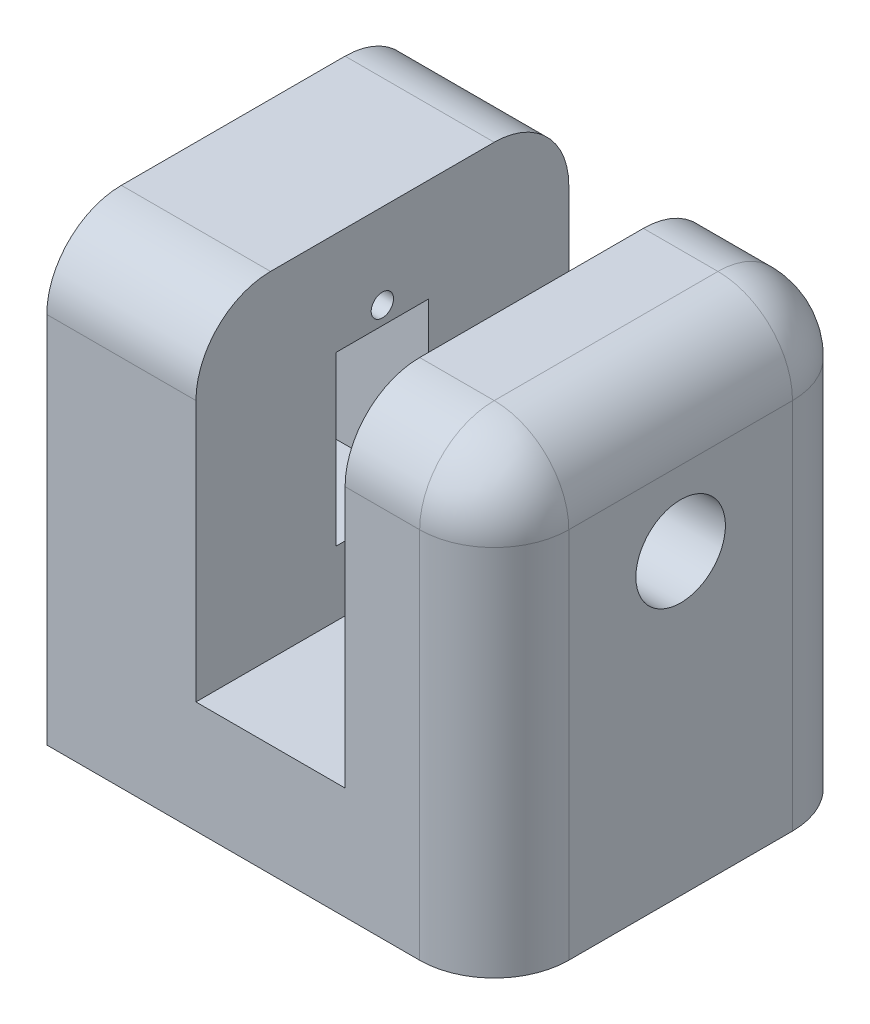
SolidWorks part; units mm, degrees
ref_plane "Front Plane" through (0, 0, 0) normal (0, 0, 1) x (1, 0, 0)
ref_plane "Top Plane" through (0, 0, 0) normal (0, 1, 0) x (1, 0, 0)
ref_plane "Right Plane" through (0, 0, 0) normal (1, 0, 0) x (0, 0, -1)
sketch "Sketch1" plane through (0, 0, 0) normal (0, 1, 0) x (1, 0, 0)
  line L1 (0, 0) -> (60, 0)
  line L2 (0, 0) -> (0, -50)
  line L3 (0, -50) -> (60, -50)
  line L4 (60, 0) -> (60, -50)
extrude "Boss-Extrude1" add sketch "Sketch1" along normal blind 15
sketch "Sketch5" plane through (0, 15, 0) normal (0, 1, 0) x (1, 0, 0)
  line L0 (0, -50) -> (60, -50) construction
  line L1 (0, 0) -> (20, 0)
  line L2 (0, 0) -> (0, -50)
  line L3 (0, -50) -> (20, -50)
  line L4 (20, 0) -> (20, -50)
  line L6 (60, 0) -> (40, 0)
  line L7 (60, 0) -> (60, -50)
  line L8 (60, -50) -> (40, -50)
  line L9 (40, 0) -> (40, -50)
extrude "Boss-Extrude5" add sketch "Sketch5" along normal blind 45
sketch "Sketch6" plane through (0, 0, 0) normal (-1, 0, 0) x (0, 0, 1)
  circle A0 centre (25, 40) radius 6
extrude "Cut-Extrude1" cut sketch "Sketch6" against normal blind 84
sketch "Sketch7" plane through (0, 0, 0) normal (0, -1, 0) x (1, 0, 0)
  circle A0 centre (30, 25) radius 2.5
extrude "Cut-Extrude2" cut sketch "Sketch7" against normal blind 19
fillet "Fillet1" radius 10 4 edges at (10, 60, 50) (50, 60, 50) (50, 60, 0) (10, 60, 0)
fillet "Fillet3" radius 10 5 edges at (60, 25, 0) (60, 57.0711, 2.9289) (60, 60, 25) (60, 57.0711, 47.0711) (60, 25, 50)
sketch "Sketch8" plane through (0, 0, 0) normal (-1, 0, 0) x (0, 0, 1)
  line L2 (25, 46.2) -> (31.2, 46.2)
  line L3 (25, 23.7) -> (18.8, 23.7)
  line L5 (31.2, 46.2) -> (18.8, 46.2)
  line L6 (31.2, 46.2) -> (31.2, 23.7)
  line L7 (31.2, 23.7) -> (18.8, 23.7)
  line L8 (18.8, 46.2) -> (18.8, 23.7)
  circle A0 centre (25, 21.3) radius 1.5
  circle A1 centre (25, 48.6) radius 1.5
  circle M13 centre (25, 40) radius 6
extrude "Cut-Extrude3" cut sketch "Sketch8" against normal blind 30 contours L5 L8 L3 L7 L6 L2 M13 | A1 | A0
